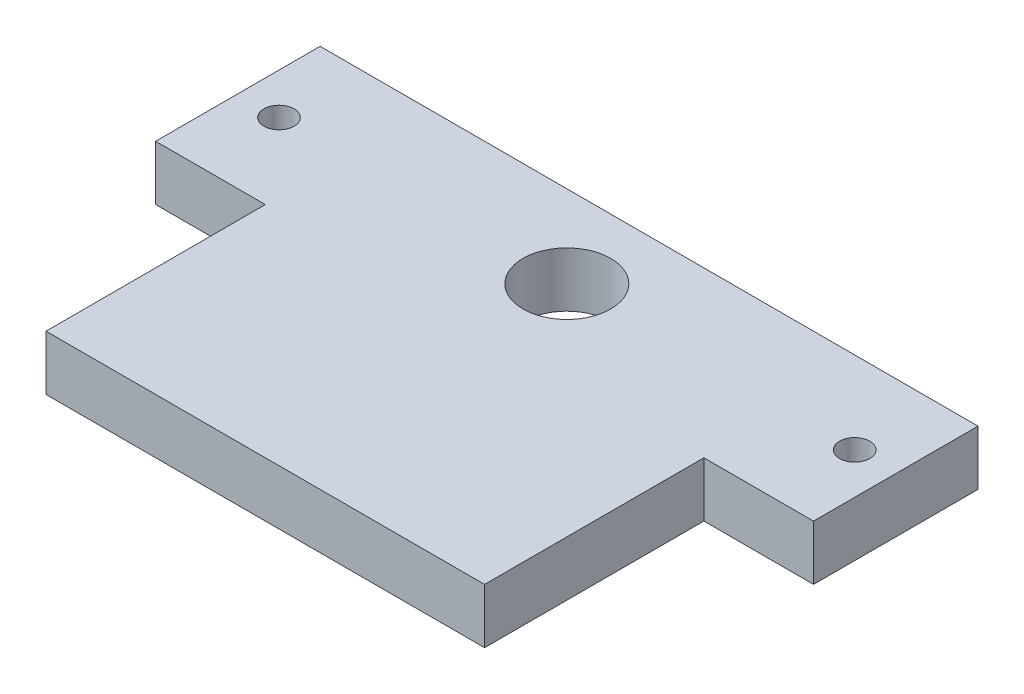
SolidWorks part; units mm, degrees
ref_plane "Front Plane" through (0, 0, 0) normal (0, 0, 1) x (1, 0, 0)
ref_plane "Top Plane" through (0, 0, 0) normal (0, 1, 0) x (1, 0, 0)
ref_plane "Right Plane" through (0, 0, 0) normal (1, 0, 0) x (0, 0, -1)
sketch "elec_bounding" plane through (0, 0, 0) normal (0, 1, 0) x (1, 0, 0)
  line L1 (-22.7987, 2.4537) -> (-18.7347, 2.4537)
  line L2 (-22.7987, 2.4537) -> (-22.7987, 0.4217)
  line L3 (-22.7987, 0.4217) -> (-18.7347, 0.4217)
  line L4 (-18.7347, 2.4537) -> (-18.7347, 0.4217)
  dimension "D1" = 4.064
  dimension "D2" = 2.032
sketch "shuttle" plane through (0, 0, 0) normal (0, 1, 0) x (1, 0, 0)
  line L0 (-22.7987, 2.4537) -> (-22.7987, 0.4217) construction
  line L1 (-23.8147, 2.4537) -> (-17.7187, 2.4537)
  line L2 (-23.8147, 2.4537) -> (-23.8147, 3.9777)
  line L3 (-23.8147, 3.9777) -> (-17.7187, 3.9777)
  line L4 (-17.7187, 2.4537) -> (-17.7187, 3.9777)
  line L5 (-18.7347, 2.4537) -> (-18.7347, 0.4217) construction
  line L6 (-22.7987, 2.4537) -> (-18.7347, 2.4537) construction
  dimension "D1" = 1.524
  dimension "D2" = 6.096
  dimension "D3" = 1.016
  dimension "D4" = 1.016
  dimension "D5" = 0
sketch "drive_screw" plane through (0, 0, 0) normal (0, 1, 0) x (1, 0, 0)
  line L0 (-18.7347, 2.4537) -> (-18.7347, 0.4217) construction
  line L2 (-22.7987, 2.4537) -> (-22.7987, 0.4217) construction
  line L3 (-23.8147, 2.4537) -> (-17.7187, 2.4537) construction
  circle A0 centre (-20.7667, 3.2157) radius 0.4064
  dimension "D1" = 2.032
  dimension "D2" = 2.032
  dimension "D3" = 0.762
sketch "guide_holes" plane through (0, 0, 0) normal (0, 1, 0) x (1, 0, 0)
  line L0 (-23.8147, 2.4537) -> (-23.8147, 3.9777) construction
  line L1 (-23.8147, 3.9777) -> (-17.7187, 3.9777) construction
  circle A0 centre (-23.4337, 3.2157) radius 0.1397
  circle A1 centre (-18.0997, 3.2157) radius 0.1397
  dimension "D1" = 0.381
  dimension "D3" = 0.762
  dimension "D2" = 2
extrude "shuttle_extr" add sketch "shuttle" against normal blind 0.508
extrude "elec_bounding_extr" add sketch "elec_bounding" against normal blind 0.508
extrude "drive_screw_extr" cut sketch "drive_screw" against normal blind 0.508
extrude "guide_holes_extr" cut sketch "guide_holes" against normal blind 0.508
sketch "electrodes" plane through (0, 0, 0) normal (0, 1, 0) x (1, 0, 0)
  circle A0 centre (-22.5521, 0.6491) radius 0.1397
  circle A1 centre (-22.0441, 0.6491) radius 0.1397
  circle A2 centre (-21.5361, 0.6491) radius 0.1397
  circle A3 centre (-21.0281, 0.6491) radius 0.1397
  circle A4 centre (-20.5201, 0.6491) radius 0.1397
  circle A5 centre (-20.0121, 0.6491) radius 0.1397
  circle A6 centre (-19.5041, 0.6491) radius 0.1397
  circle A7 centre (-18.9961, 0.6491) radius 0.1397
  circle A8 centre (-22.0441, 1.1571) radius 0.1397
  circle A9 centre (-21.5361, 1.1571) radius 0.1397
  circle A10 centre (-21.0281, 1.1571) radius 0.1397
  circle A11 centre (-20.5201, 1.1571) radius 0.1397
  circle A12 centre (-20.0121, 1.1571) radius 0.1397
  circle A13 centre (-19.5041, 1.1571) radius 0.1397
  circle A14 centre (-18.9961, 1.1571) radius 0.1397
  circle A15 centre (-22.0441, 1.6651) radius 0.1397
  circle A16 centre (-21.5361, 1.6651) radius 0.1397
  circle A17 centre (-21.0281, 1.6651) radius 0.1397
  circle A18 centre (-20.5201, 1.6651) radius 0.1397
  circle A19 centre (-20.0121, 1.6651) radius 0.1397
  circle A20 centre (-19.5041, 1.6651) radius 0.1397
  circle A21 centre (-18.9961, 1.6651) radius 0.1397
  circle A22 centre (-22.0441, 2.1731) radius 0.1397
  circle A23 centre (-21.5361, 2.1731) radius 0.1397
  circle A24 centre (-21.0281, 2.1731) radius 0.1397
  circle A25 centre (-20.5201, 2.1731) radius 0.1397
  circle A26 centre (-20.0121, 2.1731) radius 0.1397
  circle A27 centre (-19.5041, 2.1731) radius 0.1397
  circle A28 centre (-18.9961, 2.1731) radius 0.1397
  circle A29 centre (-22.5521, 1.1571) radius 0.1397
  circle A30 centre (-22.5521, 1.6651) radius 0.1397
  circle A31 centre (-22.5521, 2.1731) radius 0.1397
  dimension "D1" = 8
  dimension "D2" = 4
